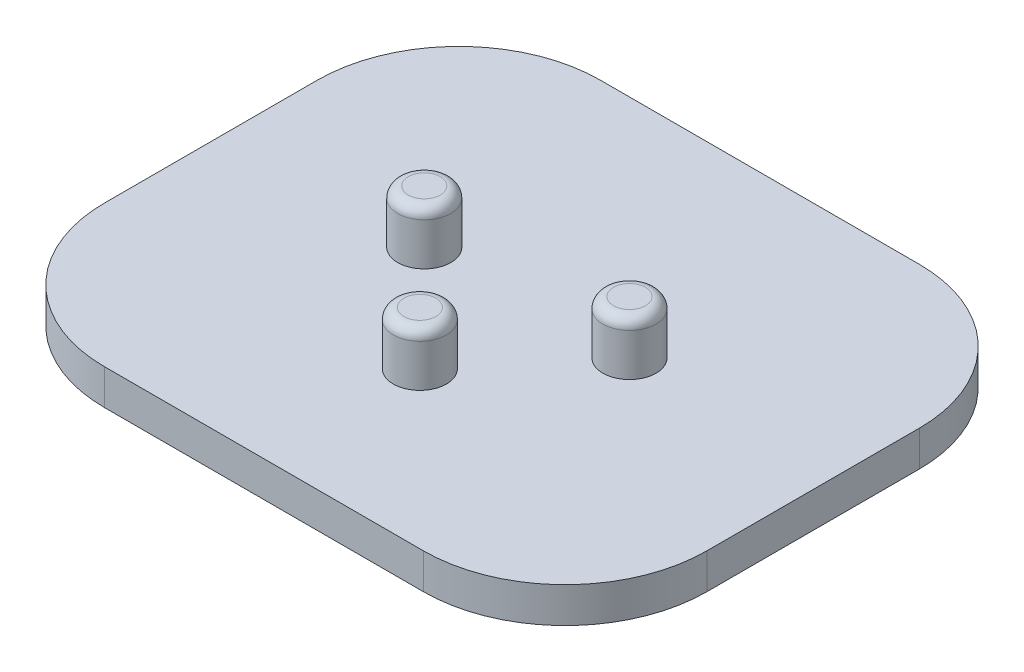
SolidWorks part; units mm, degrees
ref_plane "Front Plane" through (0, 0, 0) normal (0, 0, 1) x (1, 0, 0)
ref_plane "Top Plane" through (0, 0, 0) normal (0, 1, 0) x (1, 0, 0)
ref_plane "Right Plane" through (0, 0, 0) normal (1, 0, 0) x (0, 0, -1)
sketch "Sketch1" plane through (0, 0, 0) normal (0, 1, 0) x (1, 0, 0)
  line L1 (0, 0) -> (85, 0)
  line L2 (0, 0) -> (0, -70)
  line L3 (0, -70) -> (85, -70)
  line L4 (85, 0) -> (85, -70)
  dimension "D1" = 85
  dimension "D2" = 70
extrude "Boss-Extrude1" add sketch "Sketch1" along normal blind 5
sketch "Sketch2" plane through (0, 5, 0) normal (0, 1, 0) x (1, 0, 0)
  line L0 (42.5, -70) -> (42.5, -48)
  line L1 (0, -70) -> (85, -70) construction
  line L2 (42.5, -48) -> (55.9649, -31.8849)
  line L3 (55.9649, -31.8849) -> (27.9649, -32.8431)
  line L4 (27.9649, -32.8431) -> (42.5, -48)
  circle A0 centre (42.5, -48) radius 6
  circle A1 centre (55.9649, -31.8849) radius 10.75
  circle A2 centre (27.9649, -32.8431) radius 9
  circle A3 centre (27.9649, -32.8431) radius 3.75
  circle A4 centre (55.9649, -31.8849) radius 3.75
  circle A5 centre (42.5, -48) radius 3.75
  dimension "D2" = 12
  dimension "D3" = 18
  dimension "D4" = 21.5
  dimension "D8" = 7.5
  dimension "D9" = 7.5
  dimension "D10" = 7.5
  dimension "D1" = 22
  dimension "D5" = 28
  dimension "D6" = 21
  dimension "D7" = 21
extrude "Boss-Extrude2" add sketch "Sketch2" along normal blind 7.5 contours L3 A3 L4 | L4 A3 L3 | L3 A4 L2 | L2 A4 L3 | L0 A5 L2 | L4 A5 L0 | L2 A5 L4
fillet "Fillet1" radius 1.5 3 edges at (27.9649, 12.5, 36.5931) (55.9649, 12.5, 35.6349) (42.5, 12.5, 51.75)
fillet "Fillet2" radius 20 4 edges at (0, 2.5, 0) (85, 2.5, 0) (0, 2.5, 70) (85, 2.5, 70)
